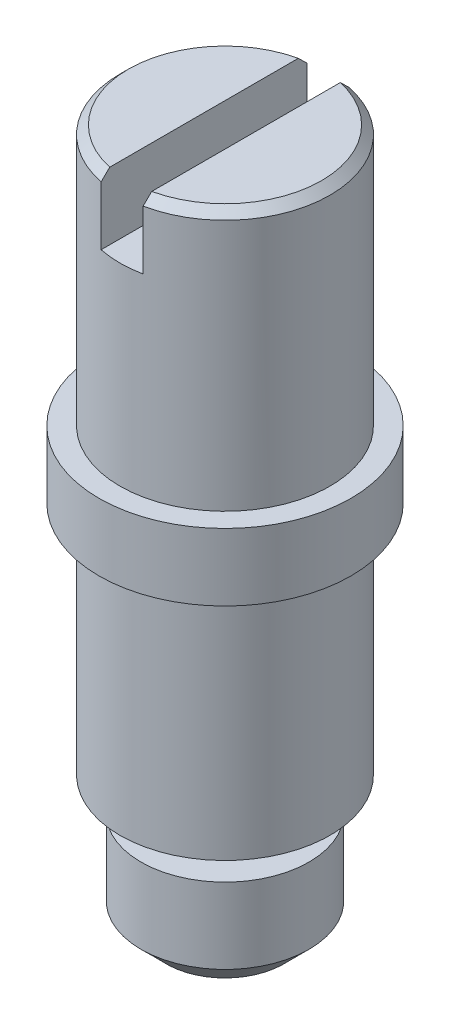
SolidWorks part; units mm, degrees
ref_plane "Alzado" through (0, 0, 0) normal (0, 0, 1) x (1, 0, 0)
ref_plane "Planta" through (0, 0, 0) normal (0, 1, 0) x (1, 0, 0)
ref_plane "Vista lateral" through (0, 0, 0) normal (1, 0, 0) x (0, 0, -1)
sketch "Sketch1" plane through (0, 0, 0) normal (0, 1, 0) x (1, 0, 0)
  circle A0 centre (0, 0) radius 0.75
  dimension "D1" = 1.5
extrude "Boss-Extrude1" add sketch "Sketch1" along normal blind 0.4
sketch "Sketch2" plane through (0, 0.4, 0) normal (0, 1, 0) x (1, 0, 0)
  circle A0 centre (0, 0) radius 0.625
  dimension "D1" = 1.25
extrude "Boss-Extrude2" add sketch "Sketch2" along normal blind 1.55
sketch "Sketch3" plane through (0, 0, 0) normal (0, 1, 0) x (1, 0, 0)
  circle A0 centre (0, 0) radius 0.625
  dimension "D1" = 1.25
extrude "Boss-Extrude3" add sketch "Sketch3" against normal blind 1.4
sketch "Sketch4" plane through (0, -1.4, 0) normal (0, -1, 0) x (1, 0, 0)
  circle A0 centre (0, 0) radius 0.3
  dimension "D1" = 0.6
extrude "Boss-Extrude4" add sketch "Sketch4" along normal blind 0.2
sketch "Sketch5" plane through (0, -1.6, 0) normal (0, -1, 0) x (1, 0, 0)
  circle A0 centre (0, 0) radius 0.5
  dimension "D1" = 1
extrude "Boss-Extrude5" add sketch "Sketch5" along normal blind 0.6
chamfer "Chamfer1" distance 0.05 angle 45 1 edges at (0, 1.95, 0.625)
chamfer "Chamfer2" distance 0.15 angle 45 1 edges at (0, -2.2, -0.5)
sketch "Sketch6" plane through (0, 0, 0) normal (0, 0, 1) x (1, 0, 0)
  line L0 (0.575, 1.95) -> (-0.575, 1.95) construction
  line L1 (0.575, 1.95) -> (-0.575, 1.95) construction
  line L2 (-1000.5161, 1.55) -> (48999.4839, 1.55) construction
  line L3 (0, -1000) -> (0, 49000) construction
  line L4 (-0.125, -999.9287) -> (-0.125, 49000.0713) construction
  line L5 (0.125, 2.1316) -> (-0.125, 2.1316)
  line L6 (0.125, 1.55) -> (0, 1.55)
  line L7 (-0.125, 2.1316) -> (-0.125, 1.55)
  line L8 (0.125, 2.1316) -> (0.125, 1.55)
  line L9 (-0.125, 1.55) -> (0, 1.55)
  point P14 (0, 2.1316)
  dimension "D1" = 0.4
  dimension "D2" = 0.125
extrude "Cut-Extrude1" cut sketch "Sketch6" against normal through all both and the other way through all
